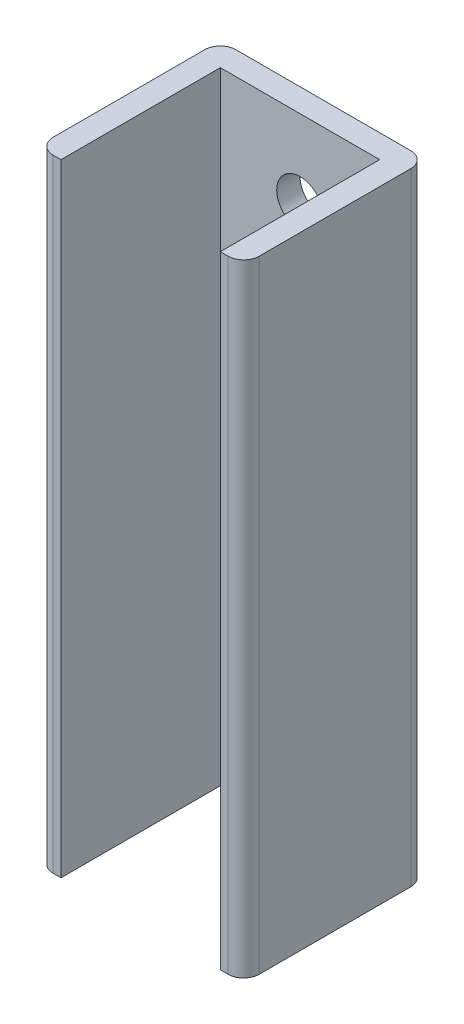
SolidWorks part; units mm, degrees
ref_plane "Front Plane" through (0, 0, 0) normal (0, 0, 1) x (1, 0, 0)
ref_plane "Top Plane" through (0, 0, 0) normal (0, 1, 0) x (1, 0, 0)
ref_plane "Right Plane" through (0, 0, 0) normal (1, 0, 0) x (0, 0, -1)
sketch "Sketch1" plane through (0, 0, 0) normal (0, 1, 0) x (1, 0, 0)
  line L0 (-11.25, 13.25) -> (11.25, 13.25)
  line L1 (-10.25, -10.25) -> (10.25, -10.25)
  line L2 (-10.25, -10.25) -> (-10.25, 10.25)
  line L3 (-10.25, 10.25) -> (10.25, 10.25)
  line L4 (10.25, -10.25) -> (10.25, 10.25)
  line L5 (-10.25, -10.25) -> (10.25, 10.25) construction
  line L6 (-10.25, 10.25) -> (10.25, -10.25) construction
  line L7 (13.25, -8.25) -> (13.25, 11.25)
  line L9 (-13.25, -8.25) -> (-13.25, 11.25)
  line L10 (-11.25, -10.25) -> (11.25, -10.25)
  line L11 (-13.25, -13.25) -> (-13.25, 13.25) construction
  line L12 (13.25, -13.25) -> (13.25, 13.25) construction
  line L13 (-13.25, -13.25) -> (13.25, -13.25) construction
  line L14 (-13.25, 13.25) -> (13.25, 13.25) construction
  arc A0 (11.25, 13.25) -> (13.25, 11.25) centre (11.25, 11.25) cw
  arc A1 (13.25, -8.25) -> (11.25, -10.25) centre (11.25, -8.25) cw
  arc A2 (-11.25, -10.25) -> (-13.25, -8.25) centre (-11.25, -8.25) cw
  arc A3 (-11.25, 13.25) -> (-13.25, 11.25) centre (-11.25, 11.25) ccw
  point P0 (0, 0)
  point P26 (0, 0)
  dimension "D4" = 2
  dimension "D1" = 20.5
  dimension "D2" = 20.5
  dimension "D3" = 3
extrude "Boss-Extrude1" add sketch "Sketch1" along normal blind 80 contours L0 A3 L9 A2 L10 L2 L3 L4 A1 L7 A0
sketch "Sketch3" plane through (0, 0, -13.25) normal (0, 0, -1) x (-1, 0, 0)
  line L0 (0, 80) -> (0, 0) construction
  line L1 (11.25, 80) -> (-11.25, 80) construction
  line L2 (11.25, 0) -> (-11.25, 0) construction
  circle A0 centre (0, 70) radius 3
  circle A1 centre (0, 10) radius 3
  point P10 (0, 0)
  point P11 (0, 0)
  point P12 (0, 0)
  dimension "D1" = 10
  dimension "D2" = 10
extrude "Cut-Extrude1" cut sketch "Sketch3" against normal blind 26
